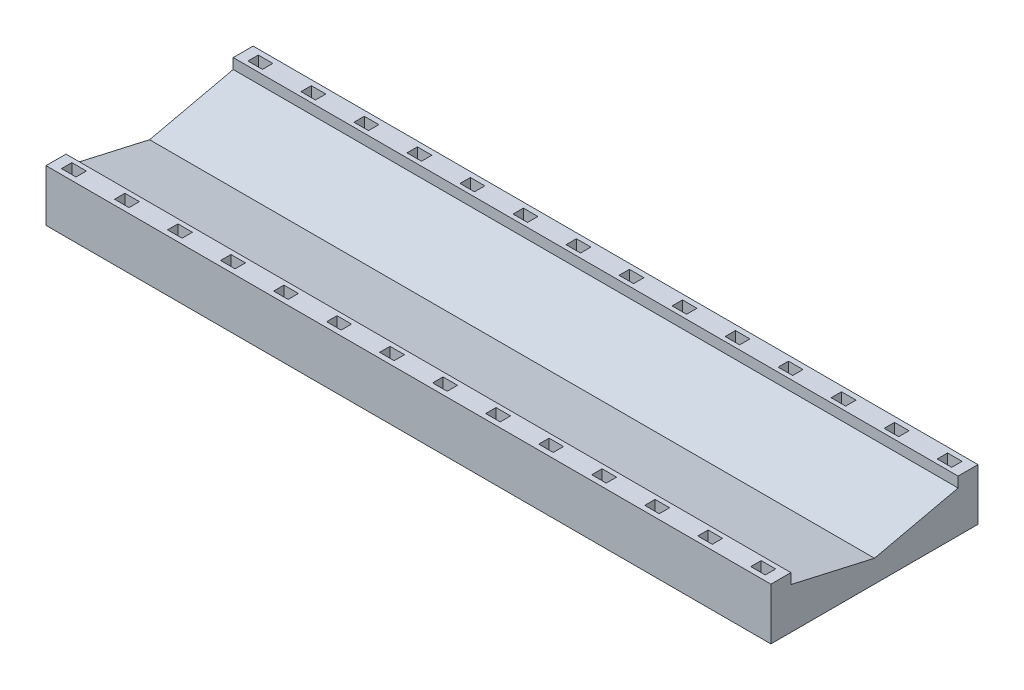
SolidWorks part; units mm, degrees
ref_plane "Front Plane" through (0, 0, 0) normal (0, 0, 1) x (1, 0, 0)
ref_plane "Top Plane" through (0, 0, 0) normal (0, 1, 0) x (1, 0, 0)
ref_plane "Right Plane" through (0, 0, 0) normal (1, 0, 0) x (0, 0, -1)
sketch "Sketch2" plane through (0, 0, 0) normal (0, 1, 0) x (1, 0, 0)
  line L1 (0, 0) -> (35, 0)
  line L2 (0, 0) -> (0, 10)
  line L3 (0, 10) -> (35, 10)
  line L4 (35, 0) -> (35, 10)
  dimension "D1" = 10
  dimension "D2" = 35
extrude "Boss-Extrude1" add sketch "Sketch2" along normal blind 2.5
sketch "Sketch3" plane through (0, 2.5, 0) normal (0, 1, 0) x (1, 0, 0)
  line L0 (0, 10) -> (0, 0) construction
  line L1 (0.5, 0.75) -> (1.2, 0.75)
  line L2 (0.5, 0.75) -> (0.5, 0.25)
  line L3 (0.5, 0.25) -> (1.2, 0.25)
  line L4 (1.2, 0.75) -> (1.2, 0.25)
  line L5 (0, 0) -> (35, 0) construction
  dimension "D1" = 0.5
  dimension "D2" = 0.7
  dimension "D3" = 0.5
  dimension "D4" = 0.25
extrude "Cut-Extrude1" cut sketch "Sketch3" against normal blind 2
pattern_linear "LPattern1" count 14 spacing 2.56 along (1, 0, 0) count 2 spacing 9 along (0, 0, -1) of "Cut-Extrude1"
sketch "Sketch4" plane through (0, 0, 0) normal (-1, 0, 0) x (0, 0, 1)
  line L0 (-9.0386, 2.5) -> (-9.0386, 2)
  line L1 (-10, 2.5) -> (0, 2.5) construction
  line L2 (-9.0386, 2) -> (-5.0019, 1.0835)
  line L3 (-5.0019, 1.0835) -> (-0.9652, 2)
  line L4 (-0.9652, 2) -> (-0.9652, 2.5)
  dimension "D1" = 0.5
  dimension "D2" = 0.5
extrude "Cut-Extrude2" cut sketch "Sketch4" against normal through all and the other way through all
